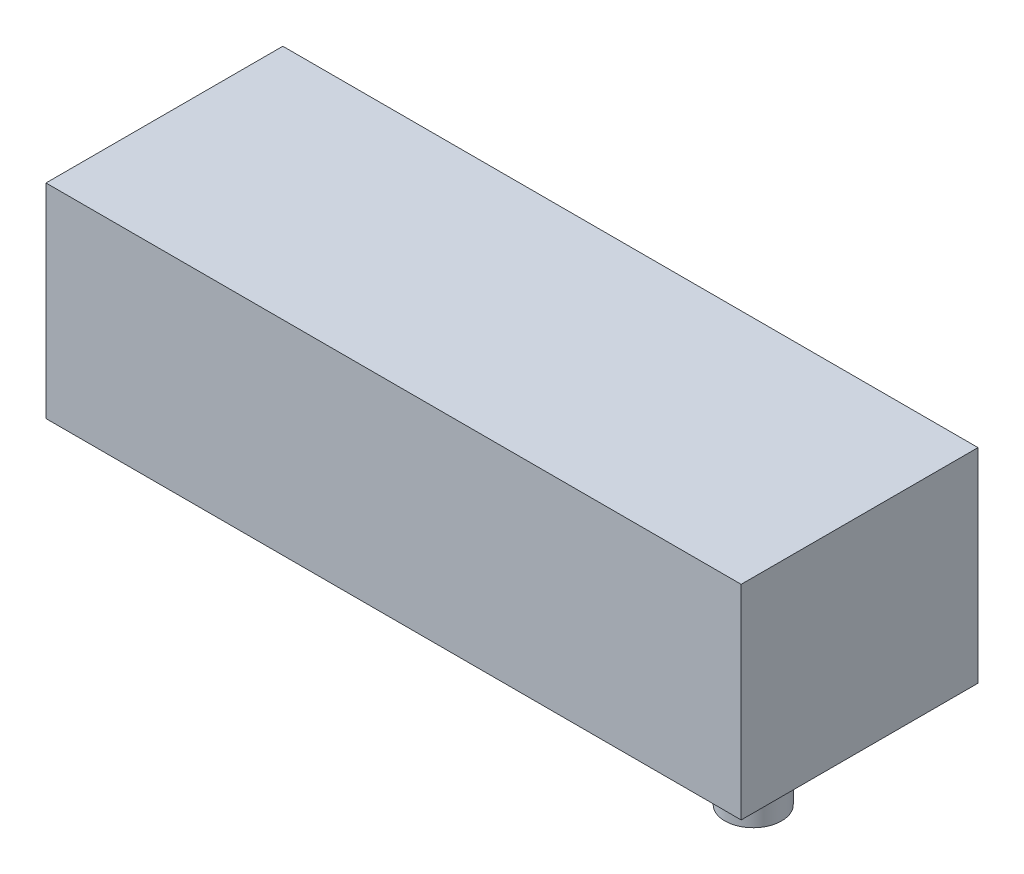
SolidWorks part; units mm, degrees
ref_plane "Front Plane" through (0, 0, 0) normal (0, 0, 1) x (1, 0, 0)
ref_plane "Top Plane" through (0, 0, 0) normal (0, 1, 0) x (1, 0, 0)
ref_plane "Right Plane" through (0, 0, 0) normal (1, 0, 0) x (0, 0, -1)
sketch "Sketch1" plane through (0, 0, 0) normal (0, 0, 1) x (1, 0, 0)
  line L1 (0, 0) -> (65.37, 0)
  line L2 (0, 0) -> (0, 19.19)
  line L3 (0, 19.19) -> (65.37, 19.19)
  line L4 (65.37, 0) -> (65.37, 19.19)
  dimension "D1" = 65.37
  dimension "D2" = 19.19
extrude "Boss-Extrude1" add sketch "Sketch1" against normal blind 22.27 contours L2 L1 L4 L3
sketch "Sketch2" plane through (0, 0, 0) normal (0, -1, 0) x (1, 0, 0)
  line L0 (65.37, -22.27) -> (65.37, 0) construction
  line L1 (55.37, 0) -> (55.37, -22.27) construction
  line L2 (0, 0) -> (65.37, 0) construction
  line L3 (0, -22.27) -> (65.37, -22.27) construction
  circle A0 centre (55.37, -11.135) radius 2.665
  point P4 (55.37, -11.135)
  dimension "D1" = 10
  dimension "D2" = 5.33
extrude "Boss-Extrude2" add sketch "Sketch2" along normal blind 9.32
